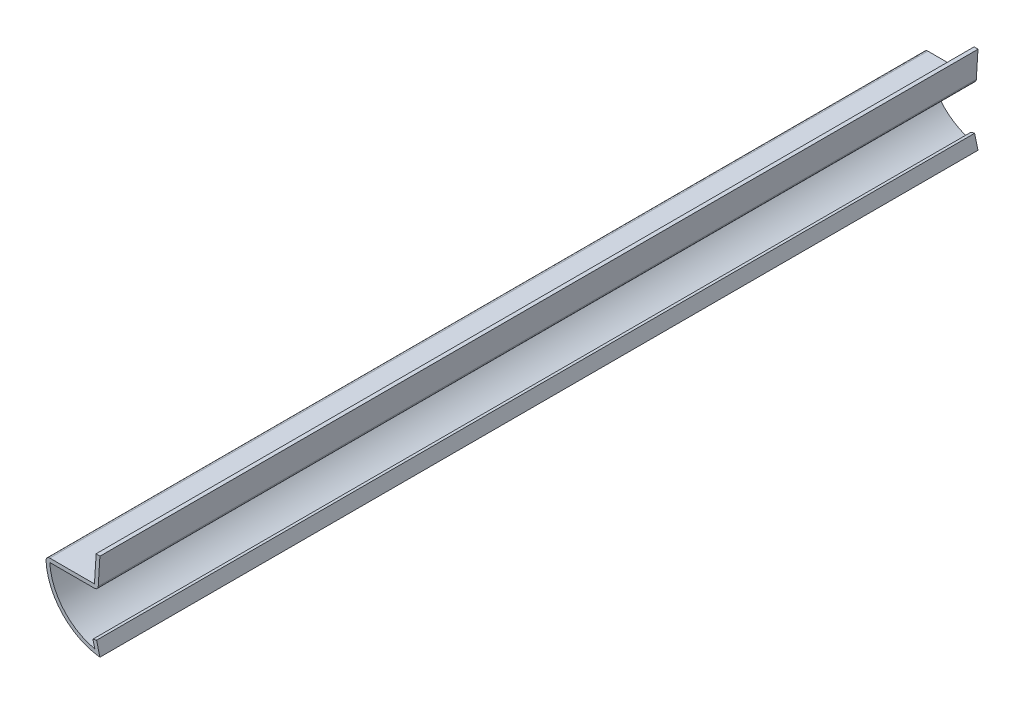
SolidWorks part; units mm, degrees
ref_plane "Front Plane" through (0, 0, 0) normal (0, 0, 1) x (1, 0, 0)
ref_plane "Top Plane" through (0, 0, 0) normal (0, 1, 0) x (1, 0, 0)
ref_plane "Right Plane" through (0, 0, 0) normal (1, 0, 0) x (0, 0, -1)
sketch "Sketch1" plane through (0, 0, 0) normal (0, 0, 1) x (1, 0, 0)
  line L0 (-0.7937, 3.0742) -> (0, 0)
  line L1 (-12.7, 14.2875) -> (-1.2859, 14.2875)
  line L2 (-1.2859, 14.2875) -> (-0.889, 20.6251)
  arc A0 (0, 0) -> (-12.7, 14.2875) centre (1.5872, 14.1991) cw
  point P3 (0, 0)
  point P8 (0, 0)
  point P9 (-1.9572, 14.1991)
  dimension "D3" = 14.2875
  dimension "D1" = 12.7
  dimension "D2" = 14.2875
  dimension "D4" = 3.175
  dimension "D5" = 6.35
  dimension "D6" = 0.3969
  dimension "D7" = 0.7937
  dimension "D8" = 0.889
extrude "Extrude-Thin1" add sketch "Sketch1" against normal blind 206.375 thin
fillet "Fillet1" radius 0.889 2 edges at (-0.4508, 13.3985, -103.1875) (-12.7, 14.2875, -103.1875)
